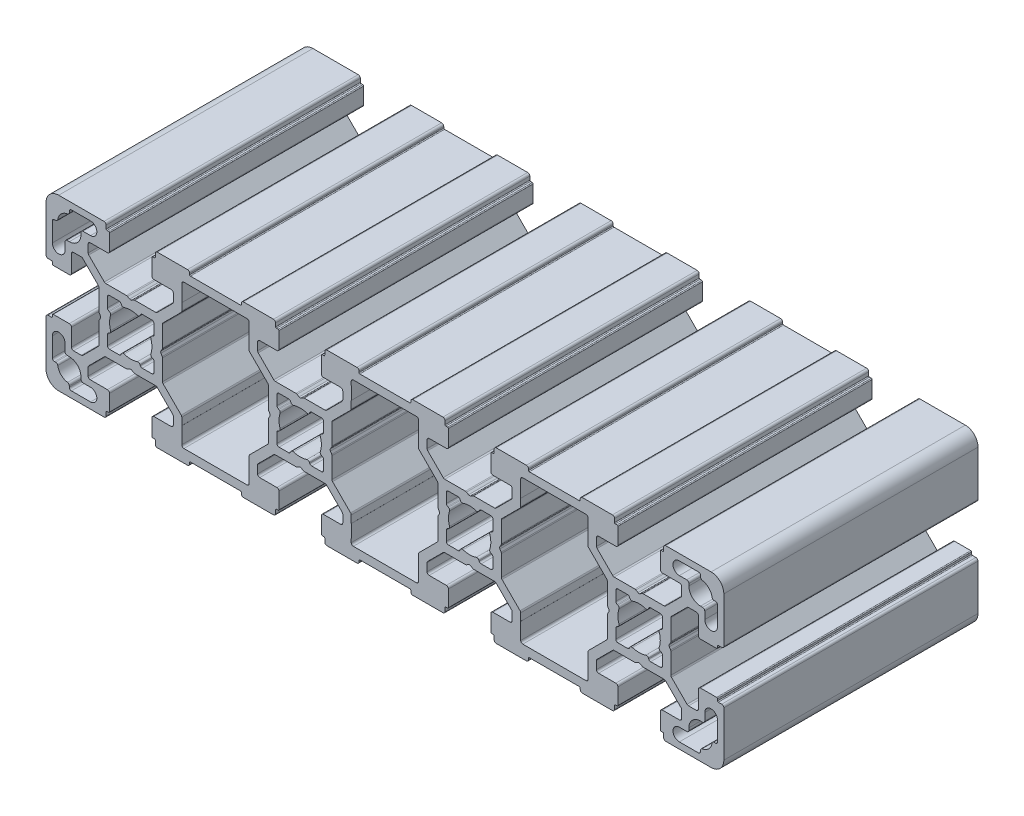
SolidWorks part; units mm, degrees
material "1060 Сплав"
ref_plane "Спереди" through (0, 0, 0) normal (0, 0, 1) x (1, 0, 0)
ref_plane "Сверху" through (0, 0, 0) normal (0, 1, 0) x (1, 0, 0)
ref_plane "Справа" through (0, 0, 0) normal (1, 0, 0) x (0, 0, -1)
sketch "Эскиз1" plane through (0, 0, 0) normal (0, 0, 1) x (1, 0, 0)
  line B0 (-95.6887, 53.3596) -> (-95.6109, 53.5385)
  line B1 (-98.4194, 53.059) -> (-96.1473, 53.059)
  line B2 (-98.9194, 55.8312) -> (-98.9194, 53.559)
  line B3 (-98.4399, 56.3675) -> (-98.6188, 56.2897)
  line B4 (-98.6188, 60.8283) -> (-98.4399, 60.7505)
  line B5 (-98.9194, 63.559) -> (-98.9194, 61.2868)
  line B6 (-96.1473, 64.059) -> (-98.4194, 64.059)
  line B7 (-95.6109, 63.5795) -> (-95.6887, 63.7584)
  line B8 (-91.1502, 63.7584) -> (-91.2279, 63.5795)
  line B9 (-88.4194, 64.059) -> (-90.6916, 64.059)
  line B10 (-87.9194, 61.2868) -> (-87.9194, 63.559)
  line B11 (-88.399, 60.7505) -> (-88.2201, 60.8283)
  line B12 (-88.2201, 56.2897) -> (-88.399, 56.3675)
  line B13 (-87.9194, 53.559) -> (-87.9194, 55.8312)
  line B14 (-90.6916, 53.059) -> (-88.4194, 53.059)
  line B15 (-91.2279, 53.5385) -> (-91.1502, 53.3596)
  line B16 (-65.323, 48.0696) -> (-61.0659, 52.3267)
  line B17 (-65.4694, 45.9733) -> (-65.4694, 47.7161)
  line B18 (-65.4844, 45.9788) -> (-65.4694, 45.9733)
  line B19 (-65.4711, 42.0607) -> (-65.4844, 45.9788)
  line B20 (-80.8677, 41.559) -> (-65.9711, 41.559)
  line B21 (-81.3544, 45.9788) -> (-81.3677, 42.0607)
  line B22 (-81.3694, 45.9733) -> (-81.3544, 45.9788)
  line B23 (-81.3694, 47.7161) -> (-81.3694, 45.9733)
  line B24 (-85.773, 52.3267) -> (-81.5159, 48.0696)
  line B25 (-85.9194, 57.559) -> (-85.9194, 52.6803)
  line B26 (-86.2751, 58.309) -> (-85.9864, 57.809)
  line B27 (-85.9864, 59.309) -> (-86.2751, 58.809)
  line B28 (-85.9194, 64.4377) -> (-85.9194, 59.559)
  line B29 (-81.5159, 69.0483) -> (-85.773, 64.7912)
  line B30 (-81.3694, 71.1446) -> (-81.3694, 69.4019)
  line B31 (-81.3544, 71.1391) -> (-81.3694, 71.1446)
  line B32 (-81.3677, 75.0573) -> (-81.3544, 71.1391)
  line B33 (-65.9711, 75.559) -> (-80.8677, 75.559)
  line B34 (-65.4844, 71.1391) -> (-65.4711, 75.0573)
  line B35 (-65.4694, 71.1446) -> (-65.4844, 71.1391)
  line B36 (-65.4694, 69.4019) -> (-65.4694, 71.1446)
  line B37 (-61.0659, 64.7912) -> (-65.323, 69.0483)
  line B38 (-60.9194, 59.559) -> (-60.9194, 64.4377)
  line B39 (-60.5638, 58.809) -> (-60.8524, 59.309)
  line B40 (-60.8524, 57.809) -> (-60.5638, 58.309)
  line B41 (-60.9194, 52.6803) -> (-60.9194, 57.559)
  line B42 (-55.6887, 53.3596) -> (-55.6109, 53.5385)
  line B43 (-58.4194, 53.059) -> (-56.1473, 53.059)
  line B44 (-58.9194, 55.8312) -> (-58.9194, 53.559)
  line B45 (-58.4399, 56.3675) -> (-58.6188, 56.2897)
  line B46 (-58.6188, 60.8283) -> (-58.4399, 60.7505)
  line B47 (-58.9194, 63.559) -> (-58.9194, 61.2868)
  line B48 (-56.1473, 64.059) -> (-58.4194, 64.059)
  line B49 (-55.6109, 63.5795) -> (-55.6887, 63.7584)
  line B50 (-51.1502, 63.7584) -> (-51.2279, 63.5795)
  line B51 (-48.4194, 64.059) -> (-50.6916, 64.059)
  line B52 (-47.9194, 61.2868) -> (-47.9194, 63.559)
  line B53 (-48.399, 60.7505) -> (-48.2201, 60.8283)
  line B54 (-48.2201, 56.2897) -> (-48.399, 56.3675)
  line B55 (-47.9194, 53.559) -> (-47.9194, 55.8312)
  line B56 (-50.6916, 53.059) -> (-48.4194, 53.059)
  line B57 (-51.2279, 53.5385) -> (-51.1502, 53.3596)
  line B58 (-25.9711, 75.559) -> (-40.8677, 75.559)
  line B59 (-25.4844, 71.1391) -> (-25.4711, 75.0573)
  line B60 (-25.4694, 71.1446) -> (-25.4844, 71.1391)
  line B61 (-25.4694, 69.4019) -> (-25.4694, 71.1446)
  line B62 (-21.0659, 64.7912) -> (-25.323, 69.0483)
  line B63 (-20.9194, 59.559) -> (-20.9194, 64.4377)
  line B64 (-20.5638, 58.809) -> (-20.8524, 59.309)
  line B65 (-20.8524, 57.809) -> (-20.5638, 58.309)
  line B66 (-20.9194, 52.6803) -> (-20.9194, 57.559)
  line B67 (-25.323, 48.0696) -> (-21.0659, 52.3267)
  line B68 (-25.4694, 45.9733) -> (-25.4694, 47.7161)
  line B69 (-25.4844, 45.9788) -> (-25.4694, 45.9733)
  line B70 (-25.4711, 42.0607) -> (-25.4844, 45.9788)
  line B71 (-40.8677, 41.559) -> (-25.9711, 41.559)
  line B72 (-41.3544, 45.9788) -> (-41.3677, 42.0607)
  line B73 (-41.3694, 45.9733) -> (-41.3544, 45.9788)
  line B74 (-41.3694, 47.7161) -> (-41.3694, 45.9733)
  line B75 (-45.773, 52.3267) -> (-41.5159, 48.0696)
  line B76 (-45.9194, 57.559) -> (-45.9194, 52.6803)
  line B77 (-46.2751, 58.309) -> (-45.9864, 57.809)
  line B78 (-45.9864, 59.309) -> (-46.2751, 58.809)
  line B79 (-45.9194, 64.4377) -> (-45.9194, 59.559)
  line B80 (-41.5159, 69.0483) -> (-45.773, 64.7912)
  line B81 (-41.3694, 71.1446) -> (-41.3694, 69.4019)
  line B82 (-41.3544, 71.1391) -> (-41.3694, 71.1446)
  line B83 (-41.3677, 75.0573) -> (-41.3544, 71.1391)
  line B84 (-27.5094, 77.559) -> (-39.3294, 77.559)
  line B85 (-39.5294, 77.759) -> (-39.5294, 78.059)
  line B86 (-40.0294, 78.559) -> (-47.1194, 78.559)
  line B87 (-47.6194, 78.059) -> (-47.6194, 77.259)
  line B88 (-47.8194, 77.059) -> (-48.2194, 77.059)
  line B89 (-48.4194, 76.859) -> (-48.4194, 73.059)
  line B90 (-47.9194, 72.559) -> (-43.8694, 72.559)
  line B91 (-43.3694, 72.059) -> (-43.3694, 70.2303)
  line B92 (-43.5159, 69.8767) -> (-47.1872, 66.2054)
  line B93 (-47.5408, 66.059) -> (-52.4194, 66.059)
  line B94 (-52.6694, 65.992) -> (-53.1694, 65.7033)
  line B95 (-53.6694, 65.7033) -> (-54.1694, 65.992)
  line B96 (-54.4194, 66.059) -> (-59.2981, 66.059)
  line B97 (-59.6517, 66.2054) -> (-63.323, 69.8767)
  line B98 (-63.4694, 70.2303) -> (-63.4694, 72.059)
  line B99 (-62.9694, 72.559) -> (-58.9194, 72.559)
  line B100 (-58.4194, 73.059) -> (-58.4194, 76.859)
  line B101 (-58.6194, 77.059) -> (-59.0194, 77.059)
  line B102 (-59.2194, 77.259) -> (-59.2194, 78.059)
  line B103 (-59.7194, 78.559) -> (-66.8094, 78.559)
  line B104 (-67.3094, 78.059) -> (-67.3094, 77.759)
  line B105 (-67.5094, 77.559) -> (-79.3294, 77.559)
  line B106 (-79.5294, 77.759) -> (-79.5294, 78.059)
  line B107 (-80.0294, 78.559) -> (-87.1194, 78.559)
  line B108 (-87.6194, 78.059) -> (-87.6194, 77.259)
  line B109 (-87.8194, 77.059) -> (-88.2194, 77.059)
  line B110 (-88.4194, 76.859) -> (-88.4194, 73.059)
  line B111 (-87.9194, 72.559) -> (-83.8694, 72.559)
  line B112 (-83.3694, 72.059) -> (-83.3694, 70.2303)
  line B113 (-83.5159, 69.8767) -> (-87.1872, 66.2054)
  line B114 (-87.5408, 66.059) -> (-92.4194, 66.059)
  line B115 (-92.6694, 65.992) -> (-93.1694, 65.7033)
  line B116 (-93.6694, 65.7033) -> (-94.1694, 65.992)
  line B117 (-94.4194, 66.059) -> (-99.2981, 66.059)
  line B118 (-99.6517, 66.2054) -> (-103.323, 69.8767)
  line B119 (-103.4694, 70.2303) -> (-103.4694, 72.059)
  line B120 (-102.9694, 72.559) -> (-98.9194, 72.559)
  line B121 (-98.4194, 73.059) -> (-98.4194, 76.859)
  line B122 (-98.6194, 77.059) -> (-99.0194, 77.059)
  line B123 (-99.2194, 77.259) -> (-99.2194, 78.059)
  line B124 (-99.7194, 78.559) -> (-110.4194, 78.559)
  line B125 (-113.4194, 75.559) -> (-113.4194, 64.859)
  line B126 (-112.9194, 64.359) -> (-112.1194, 64.359)
  line B127 (-111.9194, 64.159) -> (-111.9194, 63.759)
  line B128 (-111.7194, 63.559) -> (-107.9194, 63.559)
  line B129 (-107.4194, 64.059) -> (-107.4194, 68.109)
  line B130 (-106.9194, 68.609) -> (-105.0908, 68.609)
  line B131 (-104.7372, 68.4625) -> (-101.0659, 64.7912)
  line B132 (-100.9194, 64.4377) -> (-100.9194, 59.559)
  line B133 (-100.8524, 59.309) -> (-100.5638, 58.809)
  line B134 (-100.5638, 58.309) -> (-100.8524, 57.809)
  line B135 (-100.9194, 57.559) -> (-100.9194, 52.6803)
  line B136 (-101.0659, 52.3267) -> (-104.7372, 48.6554)
  line B137 (-105.0908, 48.509) -> (-106.9194, 48.509)
  line B138 (-107.4194, 49.009) -> (-107.4194, 53.059)
  line B139 (-107.9194, 53.559) -> (-111.7194, 53.559)
  line B140 (-111.9194, 53.359) -> (-111.9194, 52.959)
  line B141 (-112.1194, 52.759) -> (-112.9194, 52.759)
  line B142 (-113.4194, 52.259) -> (-113.4194, 41.559)
  line B143 (-110.4194, 38.559) -> (-99.7194, 38.559)
  line B144 (-99.2194, 39.059) -> (-99.2194, 39.859)
  line B145 (-99.0194, 40.059) -> (-98.6194, 40.059)
  line B146 (-98.4194, 40.259) -> (-98.4194, 44.059)
  line B147 (-98.9194, 44.559) -> (-102.9694, 44.559)
  line B148 (-103.4694, 45.059) -> (-103.4694, 46.8877)
  line B149 (-103.323, 47.2412) -> (-99.6517, 50.9125)
  line B150 (-99.2981, 51.059) -> (-94.4194, 51.059)
  line B151 (-94.1694, 51.126) -> (-93.6694, 51.4146)
  line B152 (-93.1694, 51.4146) -> (-92.6694, 51.126)
  line B153 (-92.4194, 51.059) -> (-87.5408, 51.059)
  line B154 (-87.1872, 50.9125) -> (-83.5159, 47.2412)
  line B155 (-83.3694, 46.8877) -> (-83.3694, 45.059)
  line B156 (-83.8694, 44.559) -> (-87.9194, 44.559)
  line B157 (-88.4194, 44.059) -> (-88.4194, 40.259)
  line B158 (-88.2194, 40.059) -> (-87.8194, 40.059)
  line B159 (-87.6194, 39.859) -> (-87.6194, 39.059)
  line B160 (-87.1194, 38.559) -> (-80.0294, 38.559)
  line B161 (-79.5294, 39.059) -> (-79.5294, 39.359)
  line B162 (-79.3294, 39.559) -> (-67.5094, 39.559)
  line B163 (-67.3094, 39.359) -> (-67.3094, 39.059)
  line B164 (-66.8094, 38.559) -> (-59.7194, 38.559)
  line B165 (-59.2194, 39.059) -> (-59.2194, 39.859)
  line B166 (-59.0194, 40.059) -> (-58.6194, 40.059)
  line B167 (-58.4194, 40.259) -> (-58.4194, 44.059)
  line B168 (-58.9194, 44.559) -> (-62.9694, 44.559)
  line B169 (-63.4694, 45.059) -> (-63.4694, 46.8877)
  line B170 (-63.323, 47.2412) -> (-59.6517, 50.9125)
  line B171 (-59.2981, 51.059) -> (-54.4194, 51.059)
  line B172 (-54.1694, 51.126) -> (-53.6694, 51.4146)
  line B173 (-53.1694, 51.4146) -> (-52.6694, 51.126)
  line B174 (-52.4194, 51.059) -> (-47.5408, 51.059)
  line B175 (-47.1872, 50.9125) -> (-43.5159, 47.2412)
  line B176 (-43.3694, 46.8877) -> (-43.3694, 45.059)
  line B177 (-43.8694, 44.559) -> (-47.9194, 44.559)
  line B178 (-48.4194, 44.059) -> (-48.4194, 40.259)
  line B179 (-48.2194, 40.059) -> (-47.8194, 40.059)
  line B180 (-47.6194, 39.859) -> (-47.6194, 39.059)
  line B181 (-47.1194, 38.559) -> (-40.0294, 38.559)
  line B182 (-39.5294, 39.059) -> (-39.5294, 39.359)
  line B183 (-39.3294, 39.559) -> (-27.5094, 39.559)
  line B184 (-27.3094, 39.359) -> (-27.3094, 39.059)
  line B185 (-26.8094, 38.559) -> (-19.7194, 38.559)
  line B186 (-19.2194, 39.059) -> (-19.2194, 39.859)
  line B187 (-19.0194, 40.059) -> (-18.6194, 40.059)
  line B188 (-18.4194, 40.259) -> (-18.4194, 44.059)
  line B189 (-18.9194, 44.559) -> (-22.9694, 44.559)
  line B190 (-23.4694, 45.059) -> (-23.4694, 46.8877)
  line B191 (-23.323, 47.2412) -> (-19.6517, 50.9125)
  line B192 (-19.2981, 51.059) -> (-14.4194, 51.059)
  line B193 (-14.1694, 51.126) -> (-13.6694, 51.4146)
  line B194 (-13.1694, 51.4146) -> (-12.6694, 51.126)
  line B195 (-12.4194, 51.059) -> (-7.5408, 51.059)
  line B196 (-7.1872, 50.9125) -> (-3.5159, 47.2412)
  line B197 (-3.3694, 46.8877) -> (-3.3694, 45.059)
  line B198 (-3.8694, 44.559) -> (-7.9194, 44.559)
  line B199 (-8.4194, 44.059) -> (-8.4194, 40.259)
  line B200 (-8.2194, 40.059) -> (-7.8194, 40.059)
  line B201 (-7.6194, 39.859) -> (-7.6194, 39.059)
  line B202 (-7.1194, 38.559) -> (-0.0294, 38.559)
  line B203 (0.4706, 39.059) -> (0.4706, 39.359)
  line B204 (0.6706, 39.559) -> (12.4906, 39.559)
  line B205 (12.6906, 39.359) -> (12.6906, 39.059)
  line B206 (13.1906, 38.559) -> (20.2806, 38.559)
  line B207 (20.7806, 39.059) -> (20.7806, 39.859)
  line B208 (20.9806, 40.059) -> (21.3806, 40.059)
  line B209 (21.5806, 40.259) -> (21.5806, 44.059)
  line B210 (21.0806, 44.559) -> (17.0306, 44.559)
  line B211 (16.5306, 45.059) -> (16.5306, 46.8877)
  line B212 (16.677, 47.2412) -> (20.3483, 50.9125)
  line B213 (20.7019, 51.059) -> (25.5806, 51.059)
  line B214 (25.8306, 51.126) -> (26.3306, 51.4146)
  line B215 (26.8306, 51.4146) -> (27.3306, 51.126)
  line B216 (27.5806, 51.059) -> (32.4592, 51.059)
  line B217 (32.8128, 50.9125) -> (36.4841, 47.2412)
  line B218 (36.6306, 46.8877) -> (36.6306, 45.059)
  line B219 (36.1306, 44.559) -> (32.0806, 44.559)
  line B220 (31.5806, 44.059) -> (31.5806, 40.259)
  line B221 (31.7806, 40.059) -> (32.1806, 40.059)
  line B222 (32.3806, 39.859) -> (32.3806, 39.059)
  line B223 (32.8806, 38.559) -> (43.5806, 38.559)
  line B224 (46.5806, 41.559) -> (46.5806, 52.259)
  line B225 (46.0806, 52.759) -> (45.2806, 52.759)
  line B226 (45.0806, 52.959) -> (45.0806, 53.359)
  line B227 (44.8806, 53.559) -> (41.0806, 53.559)
  line B228 (40.5806, 53.059) -> (40.5806, 49.009)
  line B229 (40.0806, 48.509) -> (38.2519, 48.509)
  line B230 (37.8983, 48.6554) -> (34.227, 52.3267)
  line B231 (34.0806, 52.6803) -> (34.0806, 57.559)
  line B232 (34.0136, 57.809) -> (33.7249, 58.309)
  line B233 (33.7249, 58.809) -> (34.0136, 59.309)
  line B234 (34.0806, 59.559) -> (34.0806, 64.4377)
  line B235 (34.227, 64.7912) -> (37.8983, 68.4625)
  line B236 (38.2519, 68.609) -> (40.0806, 68.609)
  line B237 (40.5806, 68.109) -> (40.5806, 64.059)
  line B238 (41.0806, 63.559) -> (44.8806, 63.559)
  line B239 (45.0806, 63.759) -> (45.0806, 64.159)
  line B240 (45.2806, 64.359) -> (46.0806, 64.359)
  line B241 (46.5806, 64.859) -> (46.5806, 75.559)
  line B242 (43.5806, 78.559) -> (32.8806, 78.559)
  line B243 (32.3806, 78.059) -> (32.3806, 77.259)
  line B244 (32.1806, 77.059) -> (31.7806, 77.059)
  line B245 (31.5806, 76.859) -> (31.5806, 73.059)
  line B246 (32.0806, 72.559) -> (36.1306, 72.559)
  line B247 (36.6306, 72.059) -> (36.6306, 70.2303)
  line B248 (36.4841, 69.8767) -> (32.8128, 66.2054)
  line B249 (32.4592, 66.059) -> (27.5806, 66.059)
  line B250 (27.3306, 65.992) -> (26.8306, 65.7033)
  line B251 (26.3306, 65.7033) -> (25.8306, 65.992)
  line B252 (25.5806, 66.059) -> (20.7019, 66.059)
  line B253 (20.3483, 66.2054) -> (16.677, 69.8767)
  line B254 (16.5306, 70.2303) -> (16.5306, 72.059)
  line B255 (17.0306, 72.559) -> (21.0806, 72.559)
  line B256 (21.5806, 73.059) -> (21.5806, 76.859)
  line B257 (21.3806, 77.059) -> (20.9806, 77.059)
  line B258 (20.7806, 77.259) -> (20.7806, 78.059)
  line B259 (20.2806, 78.559) -> (13.1906, 78.559)
  line B260 (12.6906, 78.059) -> (12.6906, 77.759)
  line B261 (12.4906, 77.559) -> (0.6706, 77.559)
  line B262 (0.4706, 77.759) -> (0.4706, 78.059)
  line B263 (-0.0294, 78.559) -> (-7.1194, 78.559)
  line B264 (-7.6194, 78.059) -> (-7.6194, 77.259)
  line B265 (-7.8194, 77.059) -> (-8.2194, 77.059)
  line B266 (-8.4194, 76.859) -> (-8.4194, 73.059)
  line B267 (-7.9194, 72.559) -> (-3.8694, 72.559)
  line B268 (-3.3694, 72.059) -> (-3.3694, 70.2303)
  line B269 (-3.5159, 69.8767) -> (-7.1872, 66.2054)
  line B270 (-7.5408, 66.059) -> (-12.4194, 66.059)
  line B271 (-12.6694, 65.992) -> (-13.1694, 65.7033)
  line B272 (-13.6694, 65.7033) -> (-14.1694, 65.992)
  line B273 (-14.4194, 66.059) -> (-19.2981, 66.059)
  line B274 (-19.6517, 66.2054) -> (-23.323, 69.8767)
  line B275 (-23.4694, 70.2303) -> (-23.4694, 72.059)
  line B276 (-22.9694, 72.559) -> (-18.9194, 72.559)
  line B277 (-18.4194, 73.059) -> (-18.4194, 76.859)
  line B278 (-18.6194, 77.059) -> (-19.0194, 77.059)
  line B279 (-19.2194, 77.259) -> (-19.2194, 78.059)
  line B280 (-19.7194, 78.559) -> (-26.8094, 78.559)
  line B281 (-27.3094, 78.059) -> (-27.3094, 77.759)
  line B282 (-11.1502, 63.7584) -> (-11.2279, 63.5795)
  line B283 (-8.4194, 64.059) -> (-10.6916, 64.059)
  line B284 (-7.9194, 61.2868) -> (-7.9194, 63.559)
  line B285 (-8.399, 60.7505) -> (-8.2201, 60.8283)
  line B286 (-8.2201, 56.2897) -> (-8.399, 56.3675)
  line B287 (-7.9194, 53.559) -> (-7.9194, 55.8312)
  line B288 (-10.6916, 53.059) -> (-8.4194, 53.059)
  line B289 (-11.2279, 53.5385) -> (-11.1502, 53.3596)
  line B290 (-15.6887, 53.3596) -> (-15.6109, 53.5385)
  line B291 (-18.4194, 53.059) -> (-16.1473, 53.059)
  line B292 (-18.9194, 55.8312) -> (-18.9194, 53.559)
  line B293 (-18.4399, 56.3675) -> (-18.6188, 56.2897)
  line B294 (-18.6188, 60.8283) -> (-18.4399, 60.7505)
  line B295 (-18.9194, 63.559) -> (-18.9194, 61.2868)
  line B296 (-16.1473, 64.059) -> (-18.4194, 64.059)
  line B297 (-15.6109, 63.5795) -> (-15.6887, 63.7584)
  line B298 (14.677, 48.0696) -> (18.9341, 52.3267)
  line B299 (14.5306, 45.9733) -> (14.5306, 47.7161)
  line B300 (14.5156, 45.9788) -> (14.5306, 45.9733)
  line B301 (14.5289, 42.0607) -> (14.5156, 45.9788)
  line B302 (-0.8677, 41.559) -> (14.0289, 41.559)
  line B303 (-1.3544, 45.9788) -> (-1.3677, 42.0607)
  line B304 (-1.3694, 45.9733) -> (-1.3544, 45.9788)
  line B305 (-1.3694, 47.7161) -> (-1.3694, 45.9733)
  line B306 (-5.773, 52.3267) -> (-1.5159, 48.0696)
  line B307 (-5.9194, 57.559) -> (-5.9194, 52.6803)
  line B308 (-6.2751, 58.309) -> (-5.9864, 57.809)
  line B309 (-5.9864, 59.309) -> (-6.2751, 58.809)
  line B310 (-5.9194, 64.4377) -> (-5.9194, 59.559)
  line B311 (-1.5159, 69.0483) -> (-5.773, 64.7912)
  line B312 (-1.3694, 71.1446) -> (-1.3694, 69.4019)
  line B313 (-1.3544, 71.1391) -> (-1.3694, 71.1446)
  line B314 (-1.3677, 75.0573) -> (-1.3544, 71.1391)
  line B315 (14.0289, 75.559) -> (-0.8677, 75.559)
  line B316 (14.5156, 71.1391) -> (14.5289, 75.0573)
  line B317 (14.5306, 71.1446) -> (14.5156, 71.1391)
  line B318 (14.5306, 69.4019) -> (14.5306, 71.1446)
  line B319 (18.9341, 64.7912) -> (14.677, 69.0483)
  line B320 (19.0806, 59.559) -> (19.0806, 64.4377)
  line B321 (19.4362, 58.809) -> (19.1476, 59.309)
  line B322 (19.1476, 57.809) -> (19.4362, 58.309)
  line B323 (19.0806, 52.6803) -> (19.0806, 57.559)
  line B324 (31.7799, 56.2897) -> (31.601, 56.3675)
  line B325 (32.0806, 53.559) -> (32.0806, 55.8312)
  line B326 (29.3084, 53.059) -> (31.5806, 53.059)
  line B327 (28.7721, 53.5385) -> (28.8498, 53.3596)
  line B328 (24.3113, 53.3596) -> (24.3891, 53.5385)
  line B329 (21.5806, 53.059) -> (23.8527, 53.059)
  line B330 (21.0806, 55.8312) -> (21.0806, 53.559)
  line B331 (21.5601, 56.3675) -> (21.3812, 56.2897)
  line B332 (21.3812, 60.8283) -> (21.5601, 60.7505)
  line B333 (21.0806, 63.559) -> (21.0806, 61.2868)
  line B334 (23.8527, 64.059) -> (21.5806, 64.059)
  line B335 (24.3891, 63.5795) -> (24.3113, 63.7584)
  line B336 (28.8498, 63.7584) -> (28.7721, 63.5795)
  line B337 (31.5806, 64.059) -> (29.3084, 64.059)
  line B338 (32.0806, 61.2868) -> (32.0806, 63.559)
  line B339 (31.601, 60.7505) -> (31.7799, 60.8283)
  line B340 (44.5806, 73.059) -> (44.2919, 73.059)
  line B341 (45.0806, 68.059) -> (45.0806, 72.559)
  line B342 (42.0806, 69.809) -> (42.0806, 68.059)
  line B343 (41.0806, 70.309) -> (41.5806, 70.309)
  line B344 (38.3306, 73.559) -> (38.3306, 73.059)
  line B345 (36.0806, 74.059) -> (37.8306, 74.059)
  line B346 (40.5806, 77.059) -> (36.0806, 77.059)
  line B347 (41.0806, 76.2703) -> (41.0806, 76.559)
  line B348 (44.2919, 44.059) -> (44.5806, 44.059)
  line B349 (41.0806, 40.559) -> (41.0806, 40.8477)
  line B350 (36.0806, 40.059) -> (40.5806, 40.059)
  line B351 (37.8306, 43.059) -> (36.0806, 43.059)
  line B352 (38.3306, 44.059) -> (38.3306, 43.559)
  line B353 (41.5806, 46.809) -> (41.0806, 46.809)
  line B354 (42.0806, 49.059) -> (42.0806, 47.309)
  line B355 (45.0806, 44.559) -> (45.0806, 49.059)
  line B356 (-111.4194, 44.059) -> (-111.1307, 44.059)
  line B357 (-111.9194, 49.059) -> (-111.9194, 44.559)
  line B358 (-108.9194, 47.309) -> (-108.9194, 49.059)
  line B359 (-107.9194, 46.809) -> (-108.4194, 46.809)
  line B360 (-105.1694, 43.559) -> (-105.1694, 44.059)
  line B361 (-102.9194, 43.059) -> (-104.6694, 43.059)
  line B362 (-107.4194, 40.059) -> (-102.9194, 40.059)
  line B363 (-107.9194, 40.8477) -> (-107.9194, 40.559)
  line B364 (-111.1307, 73.059) -> (-111.4194, 73.059)
  line B365 (-107.9194, 76.559) -> (-107.9194, 76.2703)
  line B366 (-102.9194, 77.059) -> (-107.4194, 77.059)
  line B367 (-104.6694, 74.059) -> (-102.9194, 74.059)
  line B368 (-105.1694, 73.059) -> (-105.1694, 73.559)
  line B369 (-108.4194, 70.309) -> (-107.9194, 70.309)
  line B370 (-108.9194, 68.059) -> (-108.9194, 69.809)
  line B371 (-111.9194, 72.559) -> (-111.9194, 68.059)
  arc B372 (-94.9949, 53.8137) -> (-91.844, 53.8137) centre (-93.4194, 58.559) ccw
  arc B373 (-94.9949, 53.8137) -> (-95.6109, 53.5385) centre (-95.1524, 53.3391) ccw
  arc B374 (-96.1473, 53.059) -> (-95.6887, 53.3596) centre (-96.1473, 53.559) ccw
  arc B375 (-98.9194, 53.559) -> (-98.4194, 53.059) centre (-98.4194, 53.559) ccw
  arc B376 (-98.6188, 56.2897) -> (-98.9194, 55.8312) centre (-98.4194, 55.8312) ccw
  arc B377 (-98.4399, 56.3675) -> (-98.1648, 56.9836) centre (-98.6393, 56.826) ccw
  arc B378 (-98.1648, 60.1344) -> (-98.1648, 56.9836) centre (-93.4194, 58.559) ccw
  arc B379 (-98.1648, 60.1344) -> (-98.4399, 60.7505) centre (-98.6393, 60.2919) ccw
  arc B380 (-98.9194, 61.2868) -> (-98.6188, 60.8283) centre (-98.4194, 61.2868) ccw
  arc B381 (-98.4194, 64.059) -> (-98.9194, 63.559) centre (-98.4194, 63.559) ccw
  arc B382 (-95.6887, 63.7584) -> (-96.1473, 64.059) centre (-96.1473, 63.559) ccw
  arc B383 (-95.6109, 63.5795) -> (-94.9949, 63.3043) centre (-95.1524, 63.7788) ccw
  arc B384 (-91.844, 63.3043) -> (-94.9949, 63.3043) centre (-93.4194, 58.559) ccw
  arc B385 (-91.844, 63.3043) -> (-91.2279, 63.5795) centre (-91.6865, 63.7788) ccw
  arc B386 (-90.6916, 64.059) -> (-91.1502, 63.7584) centre (-90.6916, 63.559) ccw
  arc B387 (-87.9194, 63.559) -> (-88.4194, 64.059) centre (-88.4194, 63.559) ccw
  arc B388 (-88.2201, 60.8283) -> (-87.9194, 61.2868) centre (-88.4194, 61.2868) ccw
  arc B389 (-88.399, 60.7505) -> (-88.6741, 60.1344) centre (-88.1996, 60.2919) ccw
  arc B390 (-88.6741, 56.9836) -> (-88.6741, 60.1344) centre (-93.4194, 58.559) ccw
  arc B391 (-88.6741, 56.9836) -> (-88.399, 56.3675) centre (-88.1996, 56.826) ccw
  arc B392 (-87.9194, 55.8312) -> (-88.2201, 56.2897) centre (-88.4194, 55.8312) ccw
  arc B393 (-88.4194, 53.059) -> (-87.9194, 53.559) centre (-88.4194, 53.559) ccw
  arc B394 (-91.1502, 53.3596) -> (-90.6916, 53.059) centre (-90.6916, 53.559) ccw
  arc B395 (-91.2279, 53.5385) -> (-91.844, 53.8137) centre (-91.6865, 53.3391) ccw
  arc B396 (-65.323, 48.0696) -> (-65.4694, 47.7161) centre (-64.9694, 47.7161) ccw
  arc B397 (-65.9711, 41.559) -> (-65.4711, 42.0607) centre (-65.9711, 42.059) ccw
  arc B398 (-81.3677, 42.0607) -> (-80.8677, 41.559) centre (-80.8677, 42.059) ccw
  arc B399 (-81.3694, 47.7161) -> (-81.5159, 48.0696) centre (-81.8694, 47.7161) ccw
  arc B400 (-85.9194, 52.6803) -> (-85.773, 52.3267) centre (-85.4194, 52.6803) ccw
  arc B401 (-85.9194, 57.559) -> (-85.9864, 57.809) centre (-86.4194, 57.559) ccw
  arc B402 (-86.2751, 58.809) -> (-86.2751, 58.309) centre (-85.8421, 58.559) ccw
  arc B403 (-85.9864, 59.309) -> (-85.9194, 59.559) centre (-86.4194, 59.559) ccw
  arc B404 (-85.773, 64.7912) -> (-85.9194, 64.4377) centre (-85.4194, 64.4377) ccw
  arc B405 (-81.5159, 69.0483) -> (-81.3694, 69.4019) centre (-81.8694, 69.4019) ccw
  arc B406 (-80.8677, 75.559) -> (-81.3677, 75.0573) centre (-80.8677, 75.059) ccw
  arc B407 (-65.4711, 75.0573) -> (-65.9711, 75.559) centre (-65.9711, 75.059) ccw
  arc B408 (-65.4694, 69.4019) -> (-65.323, 69.0483) centre (-64.9694, 69.4019) ccw
  arc B409 (-60.9194, 64.4377) -> (-61.0659, 64.7912) centre (-61.4194, 64.4377) ccw
  arc B410 (-60.9194, 59.559) -> (-60.8524, 59.309) centre (-60.4194, 59.559) ccw
  arc B411 (-60.5638, 58.309) -> (-60.5638, 58.809) centre (-60.9968, 58.559) ccw
  arc B412 (-60.8524, 57.809) -> (-60.9194, 57.559) centre (-60.4194, 57.559) ccw
  arc B413 (-61.0659, 52.3267) -> (-60.9194, 52.6803) centre (-61.4194, 52.6803) ccw
  arc B414 (-54.9949, 53.8137) -> (-51.844, 53.8137) centre (-53.4194, 58.559) ccw
  arc B415 (-54.9949, 53.8137) -> (-55.6109, 53.5385) centre (-55.1524, 53.3391) ccw
  arc B416 (-56.1473, 53.059) -> (-55.6887, 53.3596) centre (-56.1473, 53.559) ccw
  arc B417 (-58.9194, 53.559) -> (-58.4194, 53.059) centre (-58.4194, 53.559) ccw
  arc B418 (-58.6188, 56.2897) -> (-58.9194, 55.8312) centre (-58.4194, 55.8312) ccw
  arc B419 (-58.4399, 56.3675) -> (-58.1648, 56.9836) centre (-58.6393, 56.826) ccw
  arc B420 (-58.1648, 60.1344) -> (-58.1648, 56.9836) centre (-53.4194, 58.559) ccw
  arc B421 (-58.1648, 60.1344) -> (-58.4399, 60.7505) centre (-58.6393, 60.2919) ccw
  arc B422 (-58.9194, 61.2868) -> (-58.6188, 60.8283) centre (-58.4194, 61.2868) ccw
  arc B423 (-58.4194, 64.059) -> (-58.9194, 63.559) centre (-58.4194, 63.559) ccw
  arc B424 (-55.6887, 63.7584) -> (-56.1473, 64.059) centre (-56.1473, 63.559) ccw
  arc B425 (-55.6109, 63.5795) -> (-54.9949, 63.3043) centre (-55.1524, 63.7788) ccw
  arc B426 (-51.844, 63.3043) -> (-54.9949, 63.3043) centre (-53.4194, 58.559) ccw
  arc B427 (-51.844, 63.3043) -> (-51.2279, 63.5795) centre (-51.6865, 63.7788) ccw
  arc B428 (-50.6916, 64.059) -> (-51.1502, 63.7584) centre (-50.6916, 63.559) ccw
  arc B429 (-47.9194, 63.559) -> (-48.4194, 64.059) centre (-48.4194, 63.559) ccw
  arc B430 (-48.2201, 60.8283) -> (-47.9194, 61.2868) centre (-48.4194, 61.2868) ccw
  arc B431 (-48.399, 60.7505) -> (-48.6741, 60.1344) centre (-48.1996, 60.2919) ccw
  arc B432 (-48.6741, 56.9836) -> (-48.6741, 60.1344) centre (-53.4194, 58.559) ccw
  arc B433 (-48.6741, 56.9836) -> (-48.399, 56.3675) centre (-48.1996, 56.826) ccw
  arc B434 (-47.9194, 55.8312) -> (-48.2201, 56.2897) centre (-48.4194, 55.8312) ccw
  arc B435 (-48.4194, 53.059) -> (-47.9194, 53.559) centre (-48.4194, 53.559) ccw
  arc B436 (-51.1502, 53.3596) -> (-50.6916, 53.059) centre (-50.6916, 53.559) ccw
  arc B437 (-51.2279, 53.5385) -> (-51.844, 53.8137) centre (-51.6865, 53.3391) ccw
  arc B438 (-40.8677, 75.559) -> (-41.3677, 75.0573) centre (-40.8677, 75.059) ccw
  arc B439 (-25.4711, 75.0573) -> (-25.9711, 75.559) centre (-25.9711, 75.059) ccw
  arc B440 (-25.4694, 69.4019) -> (-25.323, 69.0483) centre (-24.9694, 69.4019) ccw
  arc B441 (-20.9194, 64.4377) -> (-21.0659, 64.7912) centre (-21.4194, 64.4377) ccw
  arc B442 (-20.9194, 59.559) -> (-20.8524, 59.309) centre (-20.4194, 59.559) ccw
  arc B443 (-20.5638, 58.309) -> (-20.5638, 58.809) centre (-20.9968, 58.559) ccw
  arc B444 (-20.8524, 57.809) -> (-20.9194, 57.559) centre (-20.4194, 57.559) ccw
  arc B445 (-21.0659, 52.3267) -> (-20.9194, 52.6803) centre (-21.4194, 52.6803) ccw
  arc B446 (-25.323, 48.0696) -> (-25.4694, 47.7161) centre (-24.9694, 47.7161) ccw
  arc B447 (-25.9711, 41.559) -> (-25.4711, 42.0607) centre (-25.9711, 42.059) ccw
  arc B448 (-41.3677, 42.0607) -> (-40.8677, 41.559) centre (-40.8677, 42.059) ccw
  arc B449 (-41.3694, 47.7161) -> (-41.5159, 48.0696) centre (-41.8694, 47.7161) ccw
  arc B450 (-45.9194, 52.6803) -> (-45.773, 52.3267) centre (-45.4194, 52.6803) ccw
  arc B451 (-45.9194, 57.559) -> (-45.9864, 57.809) centre (-46.4194, 57.559) ccw
  arc B452 (-46.2751, 58.809) -> (-46.2751, 58.309) centre (-45.8421, 58.559) ccw
  arc B453 (-45.9864, 59.309) -> (-45.9194, 59.559) centre (-46.4194, 59.559) ccw
  arc B454 (-45.773, 64.7912) -> (-45.9194, 64.4377) centre (-45.4194, 64.4377) ccw
  arc B455 (-41.5159, 69.0483) -> (-41.3694, 69.4019) centre (-41.8694, 69.4019) ccw
  arc B456 (-39.5294, 77.759) -> (-39.3294, 77.559) centre (-39.3294, 77.759) ccw
  arc B457 (-39.5294, 78.059) -> (-40.0294, 78.559) centre (-40.0294, 78.059) ccw
  arc B458 (-47.1194, 78.559) -> (-47.6194, 78.059) centre (-47.1194, 78.059) ccw
  arc B459 (-47.8194, 77.059) -> (-47.6194, 77.259) centre (-47.8194, 77.259) ccw
  arc B460 (-48.2194, 77.059) -> (-48.4194, 76.859) centre (-48.2194, 76.859) ccw
  arc B461 (-48.4194, 73.059) -> (-47.9194, 72.559) centre (-47.9194, 73.059) ccw
  arc B462 (-43.3694, 72.059) -> (-43.8694, 72.559) centre (-43.8694, 72.059) ccw
  arc B463 (-43.5159, 69.8767) -> (-43.3694, 70.2303) centre (-43.8694, 70.2303) ccw
  arc B464 (-47.5408, 66.059) -> (-47.1872, 66.2054) centre (-47.5408, 66.559) ccw
  arc B465 (-52.4194, 66.059) -> (-52.6694, 65.992) centre (-52.4194, 65.559) ccw
  arc B466 (-53.6694, 65.7033) -> (-53.1694, 65.7033) centre (-53.4194, 66.1363) ccw
  arc B467 (-54.1694, 65.992) -> (-54.4194, 66.059) centre (-54.4194, 65.559) ccw
  arc B468 (-59.6517, 66.2054) -> (-59.2981, 66.059) centre (-59.2981, 66.559) ccw
  arc B469 (-63.4694, 70.2303) -> (-63.323, 69.8767) centre (-62.9694, 70.2303) ccw
  arc B470 (-62.9694, 72.559) -> (-63.4694, 72.059) centre (-62.9694, 72.059) ccw
  arc B471 (-58.9194, 72.559) -> (-58.4194, 73.059) centre (-58.9194, 73.059) ccw
  arc B472 (-58.4194, 76.859) -> (-58.6194, 77.059) centre (-58.6194, 76.859) ccw
  arc B473 (-59.2194, 77.259) -> (-59.0194, 77.059) centre (-59.0194, 77.259) ccw
  arc B474 (-59.2194, 78.059) -> (-59.7194, 78.559) centre (-59.7194, 78.059) ccw
  arc B475 (-66.8094, 78.559) -> (-67.3094, 78.059) centre (-66.8094, 78.059) ccw
  arc B476 (-67.5094, 77.559) -> (-67.3094, 77.759) centre (-67.5094, 77.759) ccw
  arc B477 (-79.5294, 77.759) -> (-79.3294, 77.559) centre (-79.3294, 77.759) ccw
  arc B478 (-79.5294, 78.059) -> (-80.0294, 78.559) centre (-80.0294, 78.059) ccw
  arc B479 (-87.1194, 78.559) -> (-87.6194, 78.059) centre (-87.1194, 78.059) ccw
  arc B480 (-87.8194, 77.059) -> (-87.6194, 77.259) centre (-87.8194, 77.259) ccw
  arc B481 (-88.2194, 77.059) -> (-88.4194, 76.859) centre (-88.2194, 76.859) ccw
  arc B482 (-88.4194, 73.059) -> (-87.9194, 72.559) centre (-87.9194, 73.059) ccw
  arc B483 (-83.3694, 72.059) -> (-83.8694, 72.559) centre (-83.8694, 72.059) ccw
  arc B484 (-83.5159, 69.8767) -> (-83.3694, 70.2303) centre (-83.8694, 70.2303) ccw
  arc B485 (-87.5408, 66.059) -> (-87.1872, 66.2054) centre (-87.5408, 66.559) ccw
  arc B486 (-92.4194, 66.059) -> (-92.6694, 65.992) centre (-92.4194, 65.559) ccw
  arc B487 (-93.6694, 65.7033) -> (-93.1694, 65.7033) centre (-93.4194, 66.1363) ccw
  arc B488 (-94.1694, 65.992) -> (-94.4194, 66.059) centre (-94.4194, 65.559) ccw
  arc B489 (-99.6517, 66.2054) -> (-99.2981, 66.059) centre (-99.2981, 66.559) ccw
  arc B490 (-103.4694, 70.2303) -> (-103.323, 69.8767) centre (-102.9694, 70.2303) ccw
  arc B491 (-102.9694, 72.559) -> (-103.4694, 72.059) centre (-102.9694, 72.059) ccw
  arc B492 (-98.9194, 72.559) -> (-98.4194, 73.059) centre (-98.9194, 73.059) ccw
  arc B493 (-98.4194, 76.859) -> (-98.6194, 77.059) centre (-98.6194, 76.859) ccw
  arc B494 (-99.2194, 77.259) -> (-99.0194, 77.059) centre (-99.0194, 77.259) ccw
  arc B495 (-99.2194, 78.059) -> (-99.7194, 78.559) centre (-99.7194, 78.059) ccw
  arc B496 (-110.4194, 78.559) -> (-113.4194, 75.559) centre (-110.4194, 75.559) ccw
  arc B497 (-113.4194, 64.859) -> (-112.9194, 64.359) centre (-112.9194, 64.859) ccw
  arc B498 (-111.9194, 64.159) -> (-112.1194, 64.359) centre (-112.1194, 64.159) ccw
  arc B499 (-111.9194, 63.759) -> (-111.7194, 63.559) centre (-111.7194, 63.759) ccw
  arc B500 (-107.9194, 63.559) -> (-107.4194, 64.059) centre (-107.9194, 64.059) ccw
  arc B501 (-106.9194, 68.609) -> (-107.4194, 68.109) centre (-106.9194, 68.109) ccw
  arc B502 (-104.7372, 68.4625) -> (-105.0908, 68.609) centre (-105.0908, 68.109) ccw
  arc B503 (-100.9194, 64.4377) -> (-101.0659, 64.7912) centre (-101.4194, 64.4377) ccw
  arc B504 (-100.9194, 59.559) -> (-100.8524, 59.309) centre (-100.4194, 59.559) ccw
  arc B505 (-100.5638, 58.309) -> (-100.5638, 58.809) centre (-100.9968, 58.559) ccw
  arc B506 (-100.8524, 57.809) -> (-100.9194, 57.559) centre (-100.4194, 57.559) ccw
  arc B507 (-101.0659, 52.3267) -> (-100.9194, 52.6803) centre (-101.4194, 52.6803) ccw
  arc B508 (-105.0908, 48.509) -> (-104.7372, 48.6554) centre (-105.0908, 49.009) ccw
  arc B509 (-107.4194, 49.009) -> (-106.9194, 48.509) centre (-106.9194, 49.009) ccw
  arc B510 (-107.4194, 53.059) -> (-107.9194, 53.559) centre (-107.9194, 53.059) ccw
  arc B511 (-111.7194, 53.559) -> (-111.9194, 53.359) centre (-111.7194, 53.359) ccw
  arc B512 (-112.1194, 52.759) -> (-111.9194, 52.959) centre (-112.1194, 52.959) ccw
  arc B513 (-112.9194, 52.759) -> (-113.4194, 52.259) centre (-112.9194, 52.259) ccw
  arc B514 (-113.4194, 41.559) -> (-110.4194, 38.559) centre (-110.4194, 41.559) ccw
  arc B515 (-99.7194, 38.559) -> (-99.2194, 39.059) centre (-99.7194, 39.059) ccw
  arc B516 (-99.0194, 40.059) -> (-99.2194, 39.859) centre (-99.0194, 39.859) ccw
  arc B517 (-98.6194, 40.059) -> (-98.4194, 40.259) centre (-98.6194, 40.259) ccw
  arc B518 (-98.4194, 44.059) -> (-98.9194, 44.559) centre (-98.9194, 44.059) ccw
  arc B519 (-103.4694, 45.059) -> (-102.9694, 44.559) centre (-102.9694, 45.059) ccw
  arc B520 (-103.323, 47.2412) -> (-103.4694, 46.8877) centre (-102.9694, 46.8877) ccw
  arc B521 (-99.2981, 51.059) -> (-99.6517, 50.9125) centre (-99.2981, 50.559) ccw
  arc B522 (-94.4194, 51.059) -> (-94.1694, 51.126) centre (-94.4194, 51.559) ccw
  arc B523 (-93.1694, 51.4146) -> (-93.6694, 51.4146) centre (-93.4194, 50.9816) ccw
  arc B524 (-92.6694, 51.126) -> (-92.4194, 51.059) centre (-92.4194, 51.559) ccw
  arc B525 (-87.1872, 50.9125) -> (-87.5408, 51.059) centre (-87.5408, 50.559) ccw
  arc B526 (-83.3694, 46.8877) -> (-83.5159, 47.2412) centre (-83.8694, 46.8877) ccw
  arc B527 (-83.8694, 44.559) -> (-83.3694, 45.059) centre (-83.8694, 45.059) ccw
  arc B528 (-87.9194, 44.559) -> (-88.4194, 44.059) centre (-87.9194, 44.059) ccw
  arc B529 (-88.4194, 40.259) -> (-88.2194, 40.059) centre (-88.2194, 40.259) ccw
  arc B530 (-87.6194, 39.859) -> (-87.8194, 40.059) centre (-87.8194, 39.859) ccw
  arc B531 (-87.6194, 39.059) -> (-87.1194, 38.559) centre (-87.1194, 39.059) ccw
  arc B532 (-80.0294, 38.559) -> (-79.5294, 39.059) centre (-80.0294, 39.059) ccw
  arc B533 (-79.3294, 39.559) -> (-79.5294, 39.359) centre (-79.3294, 39.359) ccw
  arc B534 (-67.3094, 39.359) -> (-67.5094, 39.559) centre (-67.5094, 39.359) ccw
  arc B535 (-67.3094, 39.059) -> (-66.8094, 38.559) centre (-66.8094, 39.059) ccw
  arc B536 (-59.7194, 38.559) -> (-59.2194, 39.059) centre (-59.7194, 39.059) ccw
  arc B537 (-59.0194, 40.059) -> (-59.2194, 39.859) centre (-59.0194, 39.859) ccw
  arc B538 (-58.6194, 40.059) -> (-58.4194, 40.259) centre (-58.6194, 40.259) ccw
  arc B539 (-58.4194, 44.059) -> (-58.9194, 44.559) centre (-58.9194, 44.059) ccw
  arc B540 (-63.4694, 45.059) -> (-62.9694, 44.559) centre (-62.9694, 45.059) ccw
  arc B541 (-63.323, 47.2412) -> (-63.4694, 46.8877) centre (-62.9694, 46.8877) ccw
  arc B542 (-59.2981, 51.059) -> (-59.6517, 50.9125) centre (-59.2981, 50.559) ccw
  arc B543 (-54.4194, 51.059) -> (-54.1694, 51.126) centre (-54.4194, 51.559) ccw
  arc B544 (-53.1694, 51.4146) -> (-53.6694, 51.4146) centre (-53.4194, 50.9816) ccw
  arc B545 (-52.6694, 51.126) -> (-52.4194, 51.059) centre (-52.4194, 51.559) ccw
  arc B546 (-47.1872, 50.9125) -> (-47.5408, 51.059) centre (-47.5408, 50.559) ccw
  arc B547 (-43.3694, 46.8877) -> (-43.5159, 47.2412) centre (-43.8694, 46.8877) ccw
  arc B548 (-43.8694, 44.559) -> (-43.3694, 45.059) centre (-43.8694, 45.059) ccw
  arc B549 (-47.9194, 44.559) -> (-48.4194, 44.059) centre (-47.9194, 44.059) ccw
  arc B550 (-48.4194, 40.259) -> (-48.2194, 40.059) centre (-48.2194, 40.259) ccw
  arc B551 (-47.6194, 39.859) -> (-47.8194, 40.059) centre (-47.8194, 39.859) ccw
  arc B552 (-47.6194, 39.059) -> (-47.1194, 38.559) centre (-47.1194, 39.059) ccw
  arc B553 (-40.0294, 38.559) -> (-39.5294, 39.059) centre (-40.0294, 39.059) ccw
  arc B554 (-39.3294, 39.559) -> (-39.5294, 39.359) centre (-39.3294, 39.359) ccw
  arc B555 (-27.3094, 39.359) -> (-27.5094, 39.559) centre (-27.5094, 39.359) ccw
  arc B556 (-27.3094, 39.059) -> (-26.8094, 38.559) centre (-26.8094, 39.059) ccw
  arc B557 (-19.7194, 38.559) -> (-19.2194, 39.059) centre (-19.7194, 39.059) ccw
  arc B558 (-19.0194, 40.059) -> (-19.2194, 39.859) centre (-19.0194, 39.859) ccw
  arc B559 (-18.6194, 40.059) -> (-18.4194, 40.259) centre (-18.6194, 40.259) ccw
  arc B560 (-18.4194, 44.059) -> (-18.9194, 44.559) centre (-18.9194, 44.059) ccw
  arc B561 (-23.4694, 45.059) -> (-22.9694, 44.559) centre (-22.9694, 45.059) ccw
  arc B562 (-23.323, 47.2412) -> (-23.4694, 46.8877) centre (-22.9694, 46.8877) ccw
  arc B563 (-19.2981, 51.059) -> (-19.6517, 50.9125) centre (-19.2981, 50.559) ccw
  arc B564 (-14.4194, 51.059) -> (-14.1694, 51.126) centre (-14.4194, 51.559) ccw
  arc B565 (-13.1694, 51.4146) -> (-13.6694, 51.4146) centre (-13.4194, 50.9816) ccw
  arc B566 (-12.6694, 51.126) -> (-12.4194, 51.059) centre (-12.4194, 51.559) ccw
  arc B567 (-7.1872, 50.9125) -> (-7.5408, 51.059) centre (-7.5408, 50.559) ccw
  arc B568 (-3.3694, 46.8877) -> (-3.5159, 47.2412) centre (-3.8694, 46.8877) ccw
  arc B569 (-3.8694, 44.559) -> (-3.3694, 45.059) centre (-3.8694, 45.059) ccw
  arc B570 (-7.9194, 44.559) -> (-8.4194, 44.059) centre (-7.9194, 44.059) ccw
  arc B571 (-8.4194, 40.259) -> (-8.2194, 40.059) centre (-8.2194, 40.259) ccw
  arc B572 (-7.6194, 39.859) -> (-7.8194, 40.059) centre (-7.8194, 39.859) ccw
  arc B573 (-7.6194, 39.059) -> (-7.1194, 38.559) centre (-7.1194, 39.059) ccw
  arc B574 (-0.0294, 38.559) -> (0.4706, 39.059) centre (-0.0294, 39.059) ccw
  arc B575 (0.6706, 39.559) -> (0.4706, 39.359) centre (0.6706, 39.359) ccw
  arc B576 (12.6906, 39.359) -> (12.4906, 39.559) centre (12.4906, 39.359) ccw
  arc B577 (12.6906, 39.059) -> (13.1906, 38.559) centre (13.1906, 39.059) ccw
  arc B578 (20.2806, 38.559) -> (20.7806, 39.059) centre (20.2806, 39.059) ccw
  arc B579 (20.9806, 40.059) -> (20.7806, 39.859) centre (20.9806, 39.859) ccw
  arc B580 (21.3806, 40.059) -> (21.5806, 40.259) centre (21.3806, 40.259) ccw
  arc B581 (21.5806, 44.059) -> (21.0806, 44.559) centre (21.0806, 44.059) ccw
  arc B582 (16.5306, 45.059) -> (17.0306, 44.559) centre (17.0306, 45.059) ccw
  arc B583 (16.677, 47.2412) -> (16.5306, 46.8877) centre (17.0306, 46.8877) ccw
  arc B584 (20.7019, 51.059) -> (20.3483, 50.9125) centre (20.7019, 50.559) ccw
  arc B585 (25.5806, 51.059) -> (25.8306, 51.126) centre (25.5806, 51.559) ccw
  arc B586 (26.8306, 51.4146) -> (26.3306, 51.4146) centre (26.5806, 50.9816) ccw
  arc B587 (27.3306, 51.126) -> (27.5806, 51.059) centre (27.5806, 51.559) ccw
  arc B588 (32.8128, 50.9125) -> (32.4592, 51.059) centre (32.4592, 50.559) ccw
  arc B589 (36.6306, 46.8877) -> (36.4841, 47.2412) centre (36.1306, 46.8877) ccw
  arc B590 (36.1306, 44.559) -> (36.6306, 45.059) centre (36.1306, 45.059) ccw
  arc B591 (32.0806, 44.559) -> (31.5806, 44.059) centre (32.0806, 44.059) ccw
  arc B592 (31.5806, 40.259) -> (31.7806, 40.059) centre (31.7806, 40.259) ccw
  arc B593 (32.3806, 39.859) -> (32.1806, 40.059) centre (32.1806, 39.859) ccw
  arc B594 (32.3806, 39.059) -> (32.8806, 38.559) centre (32.8806, 39.059) ccw
  arc B595 (43.5806, 38.559) -> (46.5806, 41.559) centre (43.5806, 41.559) ccw
  arc B596 (46.5806, 52.259) -> (46.0806, 52.759) centre (46.0806, 52.259) ccw
  arc B597 (45.0806, 52.959) -> (45.2806, 52.759) centre (45.2806, 52.959) ccw
  arc B598 (45.0806, 53.359) -> (44.8806, 53.559) centre (44.8806, 53.359) ccw
  arc B599 (41.0806, 53.559) -> (40.5806, 53.059) centre (41.0806, 53.059) ccw
  arc B600 (40.0806, 48.509) -> (40.5806, 49.009) centre (40.0806, 49.009) ccw
  arc B601 (37.8983, 48.6554) -> (38.2519, 48.509) centre (38.2519, 49.009) ccw
  arc B602 (34.0806, 52.6803) -> (34.227, 52.3267) centre (34.5806, 52.6803) ccw
  arc B603 (34.0806, 57.559) -> (34.0136, 57.809) centre (33.5806, 57.559) ccw
  arc B604 (33.7249, 58.809) -> (33.7249, 58.309) centre (34.1579, 58.559) ccw
  arc B605 (34.0136, 59.309) -> (34.0806, 59.559) centre (33.5806, 59.559) ccw
  arc B606 (34.227, 64.7912) -> (34.0806, 64.4377) centre (34.5806, 64.4377) ccw
  arc B607 (38.2519, 68.609) -> (37.8983, 68.4625) centre (38.2519, 68.109) ccw
  arc B608 (40.5806, 68.109) -> (40.0806, 68.609) centre (40.0806, 68.109) ccw
  arc B609 (40.5806, 64.059) -> (41.0806, 63.559) centre (41.0806, 64.059) ccw
  arc B610 (44.8806, 63.559) -> (45.0806, 63.759) centre (44.8806, 63.759) ccw
  arc B611 (45.2806, 64.359) -> (45.0806, 64.159) centre (45.2806, 64.159) ccw
  arc B612 (46.0806, 64.359) -> (46.5806, 64.859) centre (46.0806, 64.859) ccw
  arc B613 (46.5806, 75.559) -> (43.5806, 78.559) centre (43.5806, 75.559) ccw
  arc B614 (32.8806, 78.559) -> (32.3806, 78.059) centre (32.8806, 78.059) ccw
  arc B615 (32.1806, 77.059) -> (32.3806, 77.259) centre (32.1806, 77.259) ccw
  arc B616 (31.7806, 77.059) -> (31.5806, 76.859) centre (31.7806, 76.859) ccw
  arc B617 (31.5806, 73.059) -> (32.0806, 72.559) centre (32.0806, 73.059) ccw
  arc B618 (36.6306, 72.059) -> (36.1306, 72.559) centre (36.1306, 72.059) ccw
  arc B619 (36.4841, 69.8767) -> (36.6306, 70.2303) centre (36.1306, 70.2303) ccw
  arc B620 (32.4592, 66.059) -> (32.8128, 66.2054) centre (32.4592, 66.559) ccw
  arc B621 (27.5806, 66.059) -> (27.3306, 65.992) centre (27.5806, 65.559) ccw
  arc B622 (26.3306, 65.7033) -> (26.8306, 65.7033) centre (26.5806, 66.1363) ccw
  arc B623 (25.8306, 65.992) -> (25.5806, 66.059) centre (25.5806, 65.559) ccw
  arc B624 (20.3483, 66.2054) -> (20.7019, 66.059) centre (20.7019, 66.559) ccw
  arc B625 (16.5306, 70.2303) -> (16.677, 69.8767) centre (17.0306, 70.2303) ccw
  arc B626 (17.0306, 72.559) -> (16.5306, 72.059) centre (17.0306, 72.059) ccw
  arc B627 (21.0806, 72.559) -> (21.5806, 73.059) centre (21.0806, 73.059) ccw
  arc B628 (21.5806, 76.859) -> (21.3806, 77.059) centre (21.3806, 76.859) ccw
  arc B629 (20.7806, 77.259) -> (20.9806, 77.059) centre (20.9806, 77.259) ccw
  arc B630 (20.7806, 78.059) -> (20.2806, 78.559) centre (20.2806, 78.059) ccw
  arc B631 (13.1906, 78.559) -> (12.6906, 78.059) centre (13.1906, 78.059) ccw
  arc B632 (12.4906, 77.559) -> (12.6906, 77.759) centre (12.4906, 77.759) ccw
  arc B633 (0.4706, 77.759) -> (0.6706, 77.559) centre (0.6706, 77.759) ccw
  arc B634 (0.4706, 78.059) -> (-0.0294, 78.559) centre (-0.0294, 78.059) ccw
  arc B635 (-7.1194, 78.559) -> (-7.6194, 78.059) centre (-7.1194, 78.059) ccw
  arc B636 (-7.8194, 77.059) -> (-7.6194, 77.259) centre (-7.8194, 77.259) ccw
  arc B637 (-8.2194, 77.059) -> (-8.4194, 76.859) centre (-8.2194, 76.859) ccw
  arc B638 (-8.4194, 73.059) -> (-7.9194, 72.559) centre (-7.9194, 73.059) ccw
  arc B639 (-3.3694, 72.059) -> (-3.8694, 72.559) centre (-3.8694, 72.059) ccw
  arc B640 (-3.5159, 69.8767) -> (-3.3694, 70.2303) centre (-3.8694, 70.2303) ccw
  arc B641 (-7.5408, 66.059) -> (-7.1872, 66.2054) centre (-7.5408, 66.559) ccw
  arc B642 (-12.4194, 66.059) -> (-12.6694, 65.992) centre (-12.4194, 65.559) ccw
  arc B643 (-13.6694, 65.7033) -> (-13.1694, 65.7033) centre (-13.4194, 66.1363) ccw
  arc B644 (-14.1694, 65.992) -> (-14.4194, 66.059) centre (-14.4194, 65.559) ccw
  arc B645 (-19.6517, 66.2054) -> (-19.2981, 66.059) centre (-19.2981, 66.559) ccw
  arc B646 (-23.4694, 70.2303) -> (-23.323, 69.8767) centre (-22.9694, 70.2303) ccw
  arc B647 (-22.9694, 72.559) -> (-23.4694, 72.059) centre (-22.9694, 72.059) ccw
  arc B648 (-18.9194, 72.559) -> (-18.4194, 73.059) centre (-18.9194, 73.059) ccw
  arc B649 (-18.4194, 76.859) -> (-18.6194, 77.059) centre (-18.6194, 76.859) ccw
  arc B650 (-19.2194, 77.259) -> (-19.0194, 77.059) centre (-19.0194, 77.259) ccw
  arc B651 (-19.2194, 78.059) -> (-19.7194, 78.559) centre (-19.7194, 78.059) ccw
  arc B652 (-26.8094, 78.559) -> (-27.3094, 78.059) centre (-26.8094, 78.059) ccw
  arc B653 (-27.5094, 77.559) -> (-27.3094, 77.759) centre (-27.5094, 77.759) ccw
  arc B654 (-11.844, 63.3043) -> (-11.2279, 63.5795) centre (-11.6865, 63.7788) ccw
  arc B655 (-10.6916, 64.059) -> (-11.1502, 63.7584) centre (-10.6916, 63.559) ccw
  arc B656 (-7.9194, 63.559) -> (-8.4194, 64.059) centre (-8.4194, 63.559) ccw
  arc B657 (-8.2201, 60.8283) -> (-7.9194, 61.2868) centre (-8.4194, 61.2868) ccw
  arc B658 (-8.399, 60.7505) -> (-8.6741, 60.1344) centre (-8.1996, 60.2919) ccw
  arc B659 (-8.6741, 56.9836) -> (-8.6741, 60.1344) centre (-13.4194, 58.559) ccw
  arc B660 (-8.6741, 56.9836) -> (-8.399, 56.3675) centre (-8.1996, 56.826) ccw
  arc B661 (-7.9194, 55.8312) -> (-8.2201, 56.2897) centre (-8.4194, 55.8312) ccw
  arc B662 (-8.4194, 53.059) -> (-7.9194, 53.559) centre (-8.4194, 53.559) ccw
  arc B663 (-11.1502, 53.3596) -> (-10.6916, 53.059) centre (-10.6916, 53.559) ccw
  arc B664 (-11.2279, 53.5385) -> (-11.844, 53.8137) centre (-11.6865, 53.3391) ccw
  arc B665 (-14.9949, 53.8137) -> (-11.844, 53.8137) centre (-13.4194, 58.559) ccw
  arc B666 (-14.9949, 53.8137) -> (-15.6109, 53.5385) centre (-15.1524, 53.3391) ccw
  arc B667 (-16.1473, 53.059) -> (-15.6887, 53.3596) centre (-16.1473, 53.559) ccw
  arc B668 (-18.9194, 53.559) -> (-18.4194, 53.059) centre (-18.4194, 53.559) ccw
  arc B669 (-18.6188, 56.2897) -> (-18.9194, 55.8312) centre (-18.4194, 55.8312) ccw
  arc B670 (-18.4399, 56.3675) -> (-18.1648, 56.9836) centre (-18.6393, 56.826) ccw
  arc B671 (-18.1648, 60.1344) -> (-18.1648, 56.9836) centre (-13.4194, 58.559) ccw
  arc B672 (-18.1648, 60.1344) -> (-18.4399, 60.7505) centre (-18.6393, 60.2919) ccw
  arc B673 (-18.9194, 61.2868) -> (-18.6188, 60.8283) centre (-18.4194, 61.2868) ccw
  arc B674 (-18.4194, 64.059) -> (-18.9194, 63.559) centre (-18.4194, 63.559) ccw
  arc B675 (-15.6887, 63.7584) -> (-16.1473, 64.059) centre (-16.1473, 63.559) ccw
  arc B676 (-15.6109, 63.5795) -> (-14.9949, 63.3043) centre (-15.1524, 63.7788) ccw
  arc B677 (-11.844, 63.3043) -> (-14.9949, 63.3043) centre (-13.4194, 58.559) ccw
  arc B678 (14.677, 48.0696) -> (14.5306, 47.7161) centre (15.0306, 47.7161) ccw
  arc B679 (14.0289, 41.559) -> (14.5289, 42.0607) centre (14.0289, 42.059) ccw
  arc B680 (-1.3677, 42.0607) -> (-0.8677, 41.559) centre (-0.8677, 42.059) ccw
  arc B681 (-1.3694, 47.7161) -> (-1.5159, 48.0696) centre (-1.8694, 47.7161) ccw
  arc B682 (-5.9194, 52.6803) -> (-5.773, 52.3267) centre (-5.4194, 52.6803) ccw
  arc B683 (-5.9194, 57.559) -> (-5.9864, 57.809) centre (-6.4194, 57.559) ccw
  arc B684 (-6.2751, 58.809) -> (-6.2751, 58.309) centre (-5.8421, 58.559) ccw
  arc B685 (-5.9864, 59.309) -> (-5.9194, 59.559) centre (-6.4194, 59.559) ccw
  arc B686 (-5.773, 64.7912) -> (-5.9194, 64.4377) centre (-5.4194, 64.4377) ccw
  arc B687 (-1.5159, 69.0483) -> (-1.3694, 69.4019) centre (-1.8694, 69.4019) ccw
  arc B688 (-0.8677, 75.559) -> (-1.3677, 75.0573) centre (-0.8677, 75.059) ccw
  arc B689 (14.5289, 75.0573) -> (14.0289, 75.559) centre (14.0289, 75.059) ccw
  arc B690 (14.5306, 69.4019) -> (14.677, 69.0483) centre (15.0306, 69.4019) ccw
  arc B691 (19.0806, 64.4377) -> (18.9341, 64.7912) centre (18.5806, 64.4377) ccw
  arc B692 (19.0806, 59.559) -> (19.1476, 59.309) centre (19.5806, 59.559) ccw
  arc B693 (19.4362, 58.309) -> (19.4362, 58.809) centre (19.0032, 58.559) ccw
  arc B694 (19.1476, 57.809) -> (19.0806, 57.559) centre (19.5806, 57.559) ccw
  arc B695 (18.9341, 52.3267) -> (19.0806, 52.6803) centre (18.5806, 52.6803) ccw
  arc B696 (41.0806, 76.2703) -> (41.5036, 75.7762) centre (41.5806, 76.2703) ccw
  arc B697 (43.7978, 73.4821) -> (41.5036, 75.7762) centre (41.0806, 73.059) ccw
  arc B698 (43.7978, 73.4821) -> (44.2919, 73.059) centre (44.2919, 73.559) ccw
  arc B699 (45.0806, 72.559) -> (44.5806, 73.059) centre (44.5806, 72.559) ccw
  arc B700 (31.601, 60.7505) -> (31.3259, 60.1344) centre (31.8004, 60.2919) ccw
  arc B701 (31.3259, 56.9836) -> (31.3259, 60.1344) centre (26.5806, 58.559) ccw
  arc B702 (31.3259, 56.9836) -> (31.601, 56.3675) centre (31.8004, 56.826) ccw
  arc B703 (32.0806, 55.8312) -> (31.7799, 56.2897) centre (31.5806, 55.8312) ccw
  arc B704 (31.5806, 53.059) -> (32.0806, 53.559) centre (31.5806, 53.559) ccw
  arc B705 (28.8498, 53.3596) -> (29.3084, 53.059) centre (29.3084, 53.559) ccw
  arc B706 (28.7721, 53.5385) -> (28.156, 53.8137) centre (28.3135, 53.3391) ccw
  arc B707 (25.0051, 53.8137) -> (28.156, 53.8137) centre (26.5806, 58.559) ccw
  arc B708 (25.0051, 53.8137) -> (24.3891, 53.5385) centre (24.8476, 53.3391) ccw
  arc B709 (23.8527, 53.059) -> (24.3113, 53.3596) centre (23.8527, 53.559) ccw
  arc B710 (21.0806, 53.559) -> (21.5806, 53.059) centre (21.5806, 53.559) ccw
  arc B711 (21.3812, 56.2897) -> (21.0806, 55.8312) centre (21.5806, 55.8312) ccw
  arc B712 (21.5601, 56.3675) -> (21.8352, 56.9836) centre (21.3607, 56.826) ccw
  arc B713 (21.8352, 60.1344) -> (21.8352, 56.9836) centre (26.5806, 58.559) ccw
  arc B714 (21.8352, 60.1344) -> (21.5601, 60.7505) centre (21.3607, 60.2919) ccw
  arc B715 (21.0806, 61.2868) -> (21.3812, 60.8283) centre (21.5806, 61.2868) ccw
  arc B716 (21.5806, 64.059) -> (21.0806, 63.559) centre (21.5806, 63.559) ccw
  arc B717 (24.3113, 63.7584) -> (23.8527, 64.059) centre (23.8527, 63.559) ccw
  arc B718 (24.3891, 63.5795) -> (25.0051, 63.3043) centre (24.8476, 63.7788) ccw
  arc B719 (28.156, 63.3043) -> (25.0051, 63.3043) centre (26.5806, 58.559) ccw
  arc B720 (28.156, 63.3043) -> (28.7721, 63.5795) centre (28.3135, 63.7788) ccw
  arc B721 (29.3084, 64.059) -> (28.8498, 63.7584) centre (29.3084, 63.559) ccw
  arc B722 (32.0806, 63.559) -> (31.5806, 64.059) centre (31.5806, 63.559) ccw
  arc B723 (31.7799, 60.8283) -> (32.0806, 61.2868) centre (31.5806, 61.2868) ccw
  arc B724 (42.0806, 68.059) -> (45.0806, 68.059) centre (43.5806, 68.059) ccw
  arc B725 (42.0806, 69.809) -> (41.5806, 70.309) centre (41.5806, 69.809) ccw
  arc B726 (38.3306, 73.059) -> (41.0806, 70.309) centre (41.0806, 73.059) ccw
  arc B727 (38.3306, 73.559) -> (37.8306, 74.059) centre (37.8306, 73.559) ccw
  arc B728 (36.0806, 77.059) -> (36.0806, 74.059) centre (36.0806, 75.559) ccw
  arc B729 (41.0806, 76.559) -> (40.5806, 77.059) centre (40.5806, 76.559) ccw
  arc B730 (44.2919, 44.059) -> (43.7978, 43.6359) centre (44.2919, 43.559) ccw
  arc B731 (41.5036, 41.3417) -> (43.7978, 43.6359) centre (41.0806, 44.059) ccw
  arc B732 (41.5036, 41.3417) -> (41.0806, 40.8477) centre (41.5806, 40.8477) ccw
  arc B733 (40.5806, 40.059) -> (41.0806, 40.559) centre (40.5806, 40.559) ccw
  arc B734 (36.0806, 43.059) -> (36.0806, 40.059) centre (36.0806, 41.559) ccw
  arc B735 (37.8306, 43.059) -> (38.3306, 43.559) centre (37.8306, 43.559) ccw
  arc B736 (41.0806, 46.809) -> (38.3306, 44.059) centre (41.0806, 44.059) ccw
  arc B737 (41.5806, 46.809) -> (42.0806, 47.309) centre (41.5806, 47.309) ccw
  arc B738 (45.0806, 49.059) -> (42.0806, 49.059) centre (43.5806, 49.059) ccw
  arc B739 (44.5806, 44.059) -> (45.0806, 44.559) centre (44.5806, 44.559) ccw
  arc B740 (-107.9194, 40.8477) -> (-108.3425, 41.3417) centre (-108.4194, 40.8477) ccw
  arc B741 (-110.6367, 43.6359) -> (-108.3425, 41.3417) centre (-107.9194, 44.059) ccw
  arc B742 (-110.6367, 43.6359) -> (-111.1307, 44.059) centre (-111.1307, 43.559) ccw
  arc B743 (-111.9194, 44.559) -> (-111.4194, 44.059) centre (-111.4194, 44.559) ccw
  arc B744 (-108.9194, 49.059) -> (-111.9194, 49.059) centre (-110.4194, 49.059) ccw
  arc B745 (-108.9194, 47.309) -> (-108.4194, 46.809) centre (-108.4194, 47.309) ccw
  arc B746 (-105.1694, 44.059) -> (-107.9194, 46.809) centre (-107.9194, 44.059) ccw
  arc B747 (-105.1694, 43.559) -> (-104.6694, 43.059) centre (-104.6694, 43.559) ccw
  arc B748 (-102.9194, 40.059) -> (-102.9194, 43.059) centre (-102.9194, 41.559) ccw
  arc B749 (-107.9194, 40.559) -> (-107.4194, 40.059) centre (-107.4194, 40.559) ccw
  arc B750 (-111.1307, 73.059) -> (-110.6367, 73.4821) centre (-111.1307, 73.559) ccw
  arc B751 (-108.3425, 75.7762) -> (-110.6367, 73.4821) centre (-107.9194, 73.059) ccw
  arc B752 (-108.3425, 75.7762) -> (-107.9194, 76.2703) centre (-108.4194, 76.2703) ccw
  arc B753 (-107.4194, 77.059) -> (-107.9194, 76.559) centre (-107.4194, 76.559) ccw
  arc B754 (-102.9194, 74.059) -> (-102.9194, 77.059) centre (-102.9194, 75.559) ccw
  arc B755 (-104.6694, 74.059) -> (-105.1694, 73.559) centre (-104.6694, 73.559) ccw
  arc B756 (-107.9194, 70.309) -> (-105.1694, 73.059) centre (-107.9194, 73.059) ccw
  arc B757 (-108.4194, 70.309) -> (-108.9194, 69.809) centre (-108.4194, 69.809) ccw
  arc B758 (-111.9194, 68.059) -> (-108.9194, 68.059) centre (-110.4194, 68.059) ccw
  arc B759 (-111.4194, 73.059) -> (-111.9194, 72.559) centre (-111.4194, 72.559) ccw
sketch_block_instance "Блок-40х160-1"
sketch_block "Блок-40х160"
extrude "Бобышка-Вытянуть1" add sketch "Эскиз1" along normal blind 60
